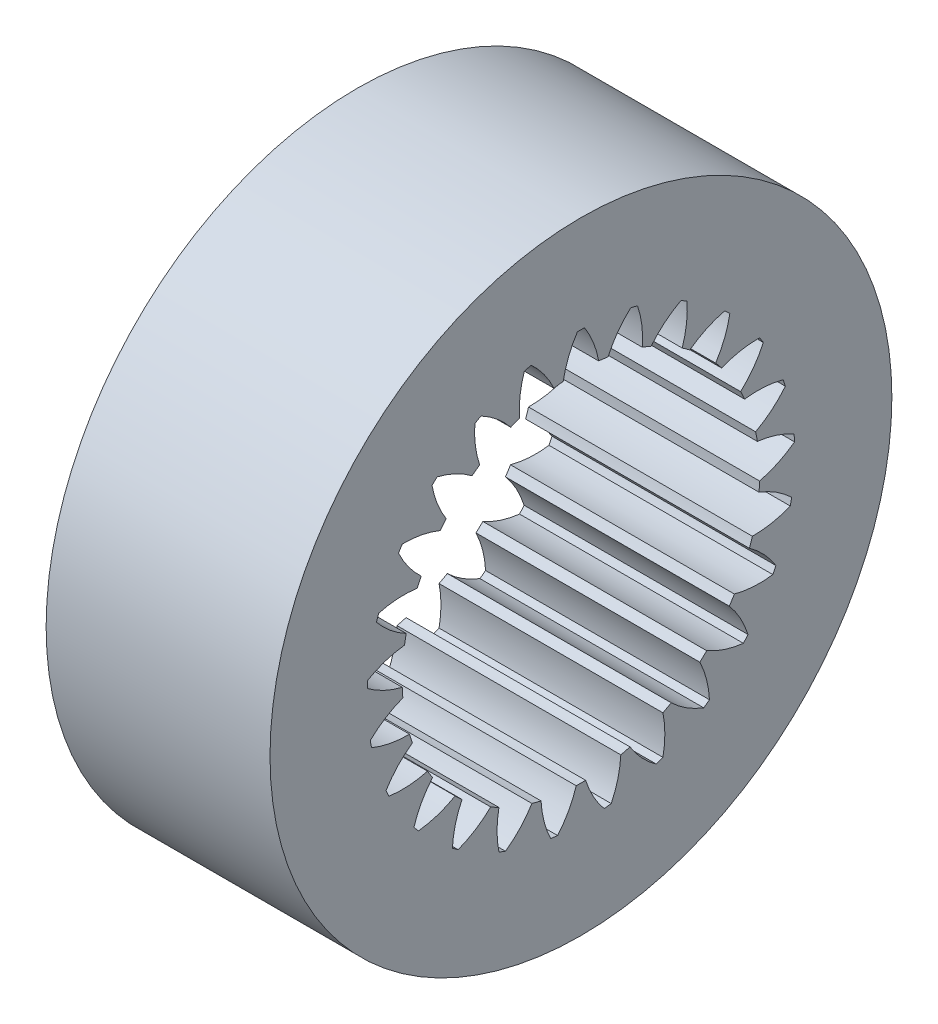
SolidWorks part; units mm, degrees
ref_plane "Front Plane" through (0, 0, 0) normal (0, 0, 1) x (1, 0, 0)
ref_plane "Top Plane" through (0, 0, 0) normal (0, 1, 0) x (1, 0, 0)
ref_plane "Right Plane" through (0, 0, 0) normal (1, 0, 0) x (0, 0, -1)
ref_plane "Plane1" through (0.8398, 0, 0) normal (1, 0, 0) x (0, 0, -1)
sketch "Sketch1" plane through (0.8398, 0, 0) normal (1, 0, 0) x (0, 0, -1)
  circle A0 centre (0.2889, 1.1711) radius 5
  arc A1 (0.7244, 4.0129) -> (1.089, 4.5152) centre (2.1459, 3.3644) cw
  arc A2 (1.089, 4.5152) -> (1.1989, 4.487) centre (0.2889, 1.1711) cw
  arc A3 (1.1989, 4.487) -> (1.2764, 3.8712) centre (-0.2817, 3.9877) cw
  arc A4 (1.2764, 3.8712) -> (1.4174, 3.8154) centre (0.2889, 1.1711) cw
  arc A5 (1.4174, 3.8154) -> (1.8955, 4.2112) centre (2.633, 2.8337) cw
  arc A6 (1.8955, 4.2112) -> (1.9949, 4.1565) centre (0.2889, 1.1711) cw
  arc A7 (1.9949, 4.1565) -> (1.9169, 3.5408) centre (0.4367, 4.0412) cw
  arc A8 (1.9169, 3.5408) -> (2.0396, 3.4517) centre (0.2889, 1.1711) cw
  arc A9 (2.0396, 3.4517) -> (2.6011, 3.7161) centre (2.9729, 2.1985) cw
  arc A10 (2.6011, 3.7161) -> (2.6838, 3.6385) centre (0.2889, 1.1711) cw
  arc A11 (2.6838, 3.6385) -> (2.4551, 3.0615) centre (1.1458, 3.9143) cw
  arc A12 (2.4551, 3.0615) -> (2.5517, 2.9446) centre (0.2889, 1.1711) cw
  arc A13 (2.5517, 2.9446) -> (3.1614, 3.0612) centre (3.1441, 1.4988) cw
  arc A14 (3.1614, 3.0612) -> (3.2222, 2.9654) centre (0.2889, 1.1711) cw
  arc A15 (3.2222, 2.9654) -> (2.8571, 2.4634) centre (1.8011, 3.615) cw
  arc A16 (2.8571, 2.4634) -> (2.9217, 2.3262) centre (0.2889, 1.1711) cw
  arc A17 (2.9217, 2.3262) -> (3.5412, 2.2875) centre (3.1359, 0.7784) cw
  arc A18 (3.5412, 2.2875) -> (3.5762, 2.1796) centre (0.2889, 1.1711) cw
  arc A19 (3.5762, 2.1796) -> (3.0978, 1.7841) centre (2.3613, 3.1621) cw
  arc A20 (3.0978, 1.7841) -> (3.1262, 1.6352) centre (0.2889, 1.1711) cw
  arc A21 (3.1262, 1.6352) -> (3.7166, 1.4436) centre (2.9488, 0.0828) cw
  arc A22 (3.7166, 1.4436) -> (3.7237, 1.3304) centre (0.2889, 1.1711) cw
  arc A23 (3.7237, 1.3304) -> (3.162, 1.0663) centre (2.7914, 2.5842) cw
  arc A24 (3.162, 1.0663) -> (3.1525, 0.915) centre (0.2889, 1.1711) cw
  arc A25 (3.1525, 0.915) -> (3.6767, 0.5826) centre (2.5945, -0.5445) cw
  arc A26 (3.6767, 0.5826) -> (3.6554, 0.4712) centre (0.2889, 1.1711) cw
  arc A27 (3.6554, 0.4712) -> (3.0457, 0.3551) centre (3.0642, 1.9175) cw
  arc A28 (3.0457, 0.3551) -> (2.9988, 0.2109) centre (0.2889, 1.1711) cw
  arc A29 (2.9988, 0.2109) -> (3.4239, -0.2414) centre (2.0955, -1.064) cw
  arc A30 (3.4239, -0.2414) -> (3.3756, -0.3441) centre (0.2889, 1.1711) cw
  arc A31 (3.3756, -0.3441) -> (2.7562, -0.3049) centre (3.1626, 1.2038) cw
  arc A32 (2.7562, -0.3049) -> (2.6749, -0.4329) centre (0.2889, 1.1711) cw
  arc A33 (2.6749, -0.4329) -> (2.9741, -0.9767) centre (1.4829, -1.443) cw
  arc A34 (2.9741, -0.9767) -> (2.9018, -1.0641) centre (0.2889, 1.1711) cw
  arc A35 (2.9018, -1.0641) -> (2.3116, -0.8721) centre (3.0805, 0.4882) cw
  arc A36 (2.3116, -0.8721) -> (2.2011, -0.9759) centre (0.2889, 1.1711) cw
  arc A37 (2.2011, -0.9759) -> (2.3557, -1.577) centre (0.7952, -1.6578) cw
  arc A38 (2.3557, -1.577) -> (2.2639, -1.6437) centre (0.2889, 1.1711) cw
  arc A39 (2.2639, -1.6437) -> (1.7399, -1.3109) centre (2.8229, -0.1846) cw
  arc A40 (1.7399, -1.3109) -> (1.6071, -1.3839) centre (0.2889, 1.1711) cw
  arc A41 (1.6071, -1.3839) -> (1.6073, -2.0046) centre (0.0758, -1.6949) cw
  arc A42 (1.6073, -2.0046) -> (1.5018, -2.0464) centre (0.2889, 1.1711) cw
  arc A43 (1.5018, -2.0464) -> (1.0771, -1.5938) centre (2.4062, -0.7722) cw
  arc A44 (1.0771, -1.5938) -> (0.9302, -1.6315) centre (0.2889, 1.1711) cw
  arc A45 (0.9302, -1.6315) -> (0.7761, -2.2327) centre (-0.6302, -1.5518) cw
  arc A46 (0.7761, -2.2327) -> (0.6636, -2.2469) centre (0.2889, 1.1711) cw
  arc A47 (0.6636, -2.2469) -> (0.3648, -1.7029) centre (1.8564, -1.2377) cw
  arc A48 (0.3648, -1.7029) -> (0.2131, -1.7029) centre (0.2889, 1.1711) cw
  arc A49 (0.2131, -1.7029) -> (-0.0857, -2.2469) centre (-1.2785, -1.2377) cw
  arc A50 (-0.0857, -2.2469) -> (-0.1982, -2.2327) centre (0.2889, 1.1711) cw
  arc A51 (-0.1982, -2.2327) -> (-0.3524, -1.6315) centre (1.2081, -1.5518) cw
  arc A52 (-0.3524, -1.6315) -> (-0.4992, -1.5938) centre (0.2889, 1.1711) cw
  arc A53 (-0.4992, -1.5938) -> (-0.9239, -2.0464) centre (-1.8283, -0.7722) cw
  arc A54 (-0.9239, -2.0464) -> (-1.0294, -2.0046) centre (0.2889, 1.1711) cw
  arc A55 (-1.0294, -2.0046) -> (-1.0292, -1.3839) centre (0.5021, -1.6949) cw
  arc A56 (-1.0292, -1.3839) -> (-1.1621, -1.3109) centre (0.2889, 1.1711) cw
  arc A57 (-1.1621, -1.3109) -> (-1.686, -1.6437) centre (-2.2451, -0.1846) cw
  arc A58 (-1.686, -1.6437) -> (-1.7778, -1.577) centre (0.2889, 1.1711) cw
  arc A59 (-1.7778, -1.577) -> (-1.6232, -0.9759) centre (-0.2174, -1.6578) cw
  arc A60 (-1.6232, -0.9759) -> (-1.7337, -0.8721) centre (0.2889, 1.1711) cw
  arc A61 (-1.7337, -0.8721) -> (-2.324, -1.0641) centre (-2.5026, 0.4882) cw
  arc A62 (-2.324, -1.0641) -> (-2.3963, -0.9767) centre (0.2889, 1.1711) cw
  arc A63 (-2.3963, -0.9767) -> (-2.097, -0.4329) centre (-0.905, -1.443) cw
  arc A64 (-2.097, -0.4329) -> (-2.1783, -0.3049) centre (0.2889, 1.1711) cw
  arc A65 (-2.1783, -0.3049) -> (-2.7977, -0.3441) centre (-2.5847, 1.2038) cw
  arc A66 (-2.7977, -0.3441) -> (-2.846, -0.2414) centre (0.2889, 1.1711) cw
  arc A67 (-2.846, -0.2414) -> (-2.421, 0.2109) centre (-1.5176, -1.064) cw
  arc A68 (-2.421, 0.2109) -> (-2.4678, 0.3551) centre (0.2889, 1.1711) cw
  arc A69 (-2.4678, 0.3551) -> (-3.0776, 0.4712) centre (-2.4863, 1.9175) cw
  arc A70 (-3.0776, 0.4712) -> (-3.0988, 0.5826) centre (0.2889, 1.1711) cw
  arc A71 (-3.0988, 0.5826) -> (-2.5746, 0.915) centre (-2.0167, -0.5445) cw
  arc A72 (-2.5746, 0.915) -> (-2.5841, 1.0663) centre (0.2889, 1.1711) cw
  arc A73 (-2.5841, 1.0663) -> (-3.1459, 1.3304) centre (-2.2135, 2.5842) cw
  arc A74 (-3.1459, 1.3304) -> (-3.1387, 1.4436) centre (0.2889, 1.1711) cw
  arc A75 (-3.1387, 1.4436) -> (-2.5484, 1.6352) centre (-2.3709, 0.0828) cw
  arc A76 (-2.5484, 1.6352) -> (-2.5199, 1.7841) centre (0.2889, 1.1711) cw
  arc A77 (-2.5199, 1.7841) -> (-2.9984, 2.1796) centre (-1.7835, 3.1621) cw
  arc A78 (-2.9984, 2.1796) -> (-2.9633, 2.2875) centre (0.2889, 1.1711) cw
  arc A79 (-2.9633, 2.2875) -> (-2.3438, 2.3262) centre (-2.558, 0.7784) cw
  arc A80 (-2.3438, 2.3262) -> (-2.2793, 2.4634) centre (0.2889, 1.1711) cw
  arc A81 (-2.2793, 2.4634) -> (-2.6443, 2.9654) centre (-1.2232, 3.615) cw
  arc A82 (-2.6443, 2.9654) -> (-2.5835, 3.0612) centre (0.2889, 1.1711) cw
  arc A83 (-2.5835, 3.0612) -> (-1.9738, 2.9446) centre (-2.5662, 1.4988) cw
  arc A84 (-1.9738, 2.9446) -> (-1.8772, 3.0615) centre (0.2889, 1.1711) cw
  arc A85 (-1.8772, 3.0615) -> (-2.1059, 3.6385) centre (-0.5679, 3.9143) cw
  arc A86 (-2.1059, 3.6385) -> (-2.0232, 3.7161) centre (0.2889, 1.1711) cw
  arc A87 (-2.0232, 3.7161) -> (-1.4617, 3.4517) centre (-2.395, 2.1985) cw
  arc A88 (-1.4617, 3.4517) -> (-1.339, 3.5408) centre (0.2889, 1.1711) cw
  arc A89 (-1.339, 3.5408) -> (-1.417, 4.1565) centre (0.1412, 4.0412) cw
  arc A90 (-1.417, 4.1565) -> (-1.3176, 4.2112) centre (0.2889, 1.1711) cw
  arc A91 (-1.3176, 4.2112) -> (-0.8395, 3.8154) centre (-2.0552, 2.8337) cw
  arc A92 (-0.8395, 3.8154) -> (-0.6986, 3.8712) centre (0.2889, 1.1711) cw
  arc A93 (-0.6986, 3.8712) -> (-0.621, 4.487) centre (0.8596, 3.9877) cw
  arc A94 (-0.621, 4.487) -> (-0.5111, 4.5152) centre (0.2889, 1.1711) cw
  arc A95 (-0.5111, 4.5152) -> (-0.1465, 4.0129) centre (-1.568, 3.3644) cw
  arc A96 (-0.1465, 4.0129) -> (0.0039, 4.0319) centre (0.2889, 1.1711) cw
  arc A97 (0.0039, 4.0319) -> (0.2322, 4.6091) centre (1.5421, 3.7573) cw
  arc A98 (0.2322, 4.6091) -> (0.3457, 4.6091) centre (0.2889, 1.1711) cw
  arc A99 (0.3457, 4.6091) -> (0.5739, 4.0319) centre (-0.9642, 3.7573) cw
  arc A100 (0.5739, 4.0319) -> (0.7244, 4.0129) centre (0.2889, 1.1711) cw
extrude "Boss-Extrude1" add sketch "Sketch1" against normal blind 3.6
